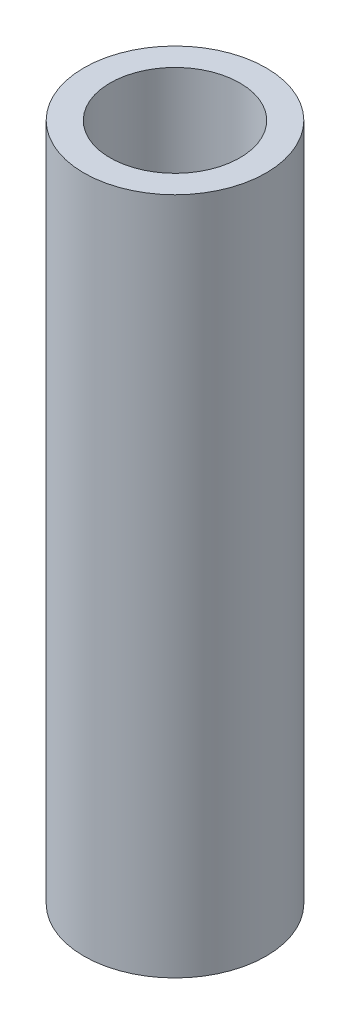
SolidWorks part; units mm, degrees
material "Acrylic (Medium-high impact)"
ref_plane "Front Plane" through (0, 0, 0) normal (0, 0, 1) x (1, 0, 0)
ref_plane "Top Plane" through (0, 0, 0) normal (0, 1, 0) x (1, 0, 0)
ref_plane "Right Plane" through (0, 0, 0) normal (1, 0, 0) x (0, 0, -1)
sketch "Sketch2" plane through (0, 0, 0) normal (0, -1, 0) x (1, 0, 0)
  circle A0 centre (0, 0) radius 9.2799
  circle A1 centre (0, 0) radius 6.6091
extrude "Boss-Extrude1" add sketch "Sketch2" along normal blind 69.088
